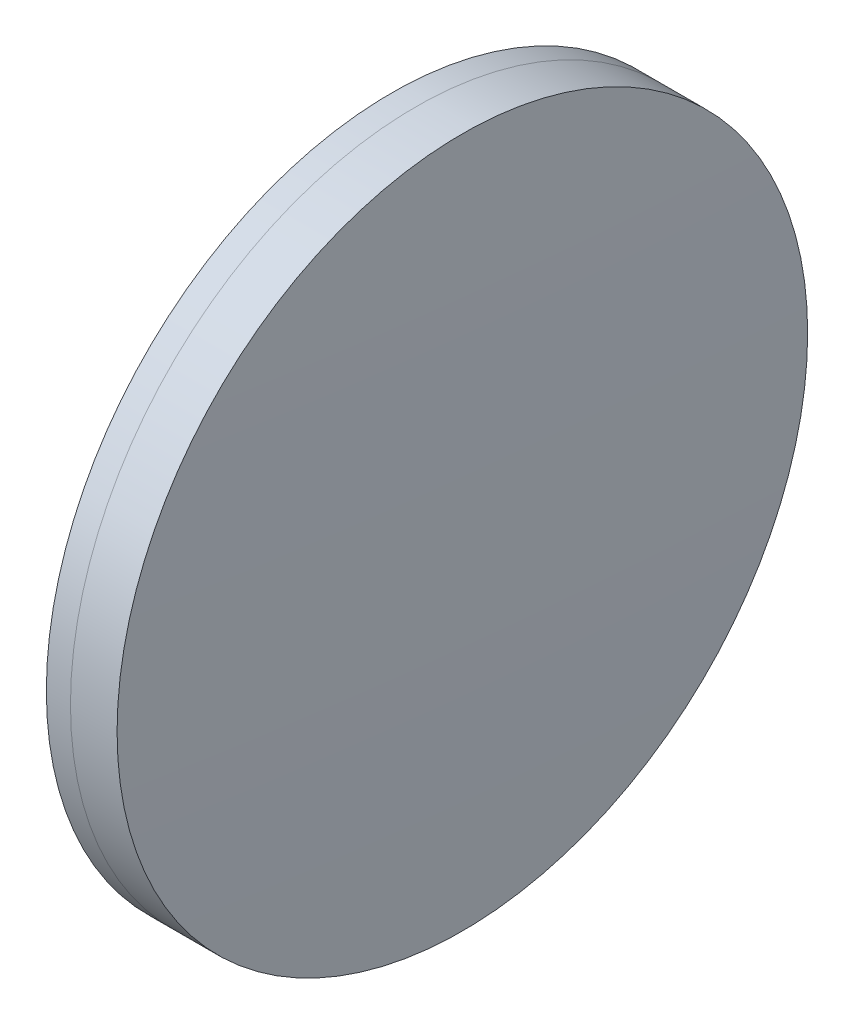
SolidWorks part; units mm, degrees
ref_plane "前视基准面" through (0, 0, 0) normal (0, 0, 1) x (1, 0, 0)
ref_plane "上视基准面" through (0, 0, 0) normal (0, 1, 0) x (1, 0, 0)
ref_plane "右视基准面" through (0, 0, 0) normal (1, 0, 0) x (0, 0, -1)
sketch "草图1" plane through (0, 0, 0) normal (0, 1, 0) x (1, 0, 0)
  line L0 (124.5233, 0) -> (395.1269, 0) construction
  line L1 (291.915, -25) -> (293.6613, -25)
  line L2 (291.915, 25) -> (293.6613, 25)
  arc A0 (293.6613, -25) -> (293.6613, 25) centre (39.5551, 0) ccw
  arc A1 (291.915, 25) -> (291.915, -25) centre (678.8101, 0) ccw
  point P10 (291.1081, 0)
  point P11 (294.8881, 0)
  dimension "D3" = 387.702
  dimension "D4" = 255.333
  dimension "D1" = 25
  dimension "D2" = 25
  dimension "D5" = 3.78
revolve "旋转1" add sketch "草图1" angle 360 about L0
sketch "草图2" plane through (0, 0, 0) normal (0, 1, 0) x (1, 0, 0)
  line L0 (-0.5519, 0) -> (409.4962, 0) construction
  line L2 (293.6613, 25) -> (297.0363, 25)
  line L3 (293.6613, -25) -> (297.0363, -25)
  arc A0 (297.0363, -25) -> (297.0363, 25) centre (-543.2889, 0) ccw
  arc A1 (293.6613, -25) -> (293.6613, 25) centre (39.5551, 0) ccw construction
  arc A2 (293.6613, -25) -> (293.6613, 25) centre (39.5551, 0) ccw
  point P4 (294.8881, 0)
  point P8 (297.4081, 0)
  dimension "D1" = 840.697
  dimension "D2" = 2.52
revolve "旋转3" add sketch "草图2" angle 360 about L0
